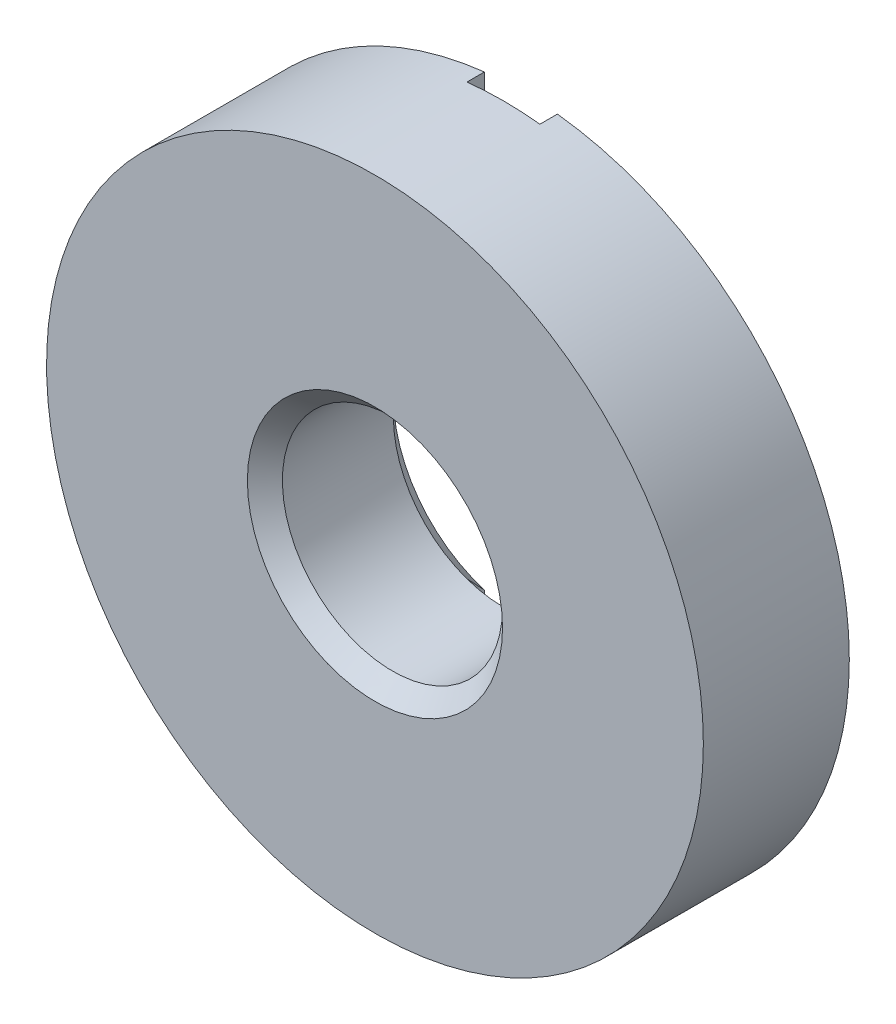
SolidWorks part; units mm, degrees
material "304, 316 OR 302 SSTL"
ref_plane "XY" through (0, 0, 0) normal (0, 0, 1) x (1, 0, 0)
ref_plane "XZ" through (0, 0, 0) normal (0, 1, 0) x (1, 0, 0)
ref_plane "YZ" through (0, 0, 0) normal (1, 0, 0) x (0, 0, -1)
sketch "Sketch1" plane through (0, 0, 0) normal (0, 0, 1) x (1, 0, 0)
  circle A0 centre (0, 0) radius 4.7879
  circle A1 centre (0, 0) radius 14.2875
  dimension "D1" = 9.5758
  dimension "D2" = 28.575
extrude "Extrude1" add sketch "Sketch1" along normal blind 6.35
chamfer "Chamfer2" distance 0.762 angle 45
sketch "Sketch2" plane through (0, 0, 0) normal (0, 0, -1) x (-1, 0, 0)
  line L0 (-1.5875, 14.2875) -> (1.5875, -14.2875) construction
  line L1 (-1.5875, 14.2875) -> (1.5875, 14.2875)
  line L2 (-1.5875, 14.2875) -> (-1.5875, -14.2875)
  line L3 (-1.5875, -14.2875) -> (1.5875, -14.2875)
  line L4 (1.5875, 14.2875) -> (1.5875, -14.2875)
  circle A0 centre (0, 0) radius 14.2875 construction
  dimension "D1" = 3.175
extrude "Cut-Extrude1" cut sketch "Sketch2" against normal blind 0.762
